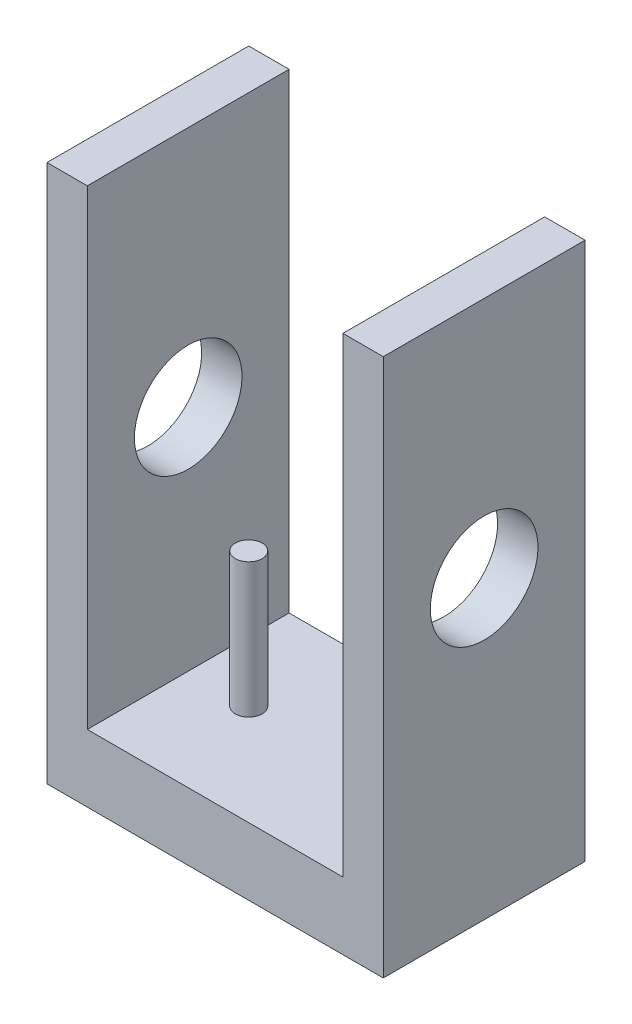
SolidWorks part; units mm, degrees
ref_plane "Plan de face" through (0, 0, 0) normal (0, 0, 1) x (1, 0, 0)
ref_plane "Plan de dessus" through (0, 0, 0) normal (0, 1, 0) x (1, 0, 0)
ref_plane "Plan de droite" through (0, 0, 0) normal (1, 0, 0) x (0, 0, -1)
sketch "Esquisse1" plane through (0, 0, 0) normal (0, 0, 1) x (1, 0, 0)
  line L1 (0, 0) -> (25, 0)
  line L2 (0, 0) -> (0, -40)
  line L3 (0, -40) -> (25, -40)
  line L4 (25, 0) -> (25, -40)
  dimension "D1" = 40
  dimension "D2" = 25
extrude "Boss.-Extru.2" add sketch "Esquisse1" along normal blind 15
sketch "Esquisse3" plane through (0, 0, 0) normal (0, 0, 1) x (1, 0, 0)
  line L0 (25, 0) -> (0, 0) construction
  line L1 (3, 0) -> (22, 0)
  line L2 (3, 0) -> (3, -35)
  line L3 (3, -35) -> (22, -35)
  line L4 (22, 0) -> (22, -35)
  line L5 (0, 0) -> (0, -40) construction
  line L6 (25, -40) -> (25, 0) construction
  line L7 (0, -40) -> (25, -40) construction
  dimension "D1" = 3
  dimension "D2" = 3
  dimension "D3" = 5
extrude "Enlèv. mat.-Extru.4" cut sketch "Esquisse3" along normal through all
sketch "Esquisse4" plane through (0, -35, 0) normal (0, 1, 0) x (1, 0, 0)
  line L0 (25, -15) -> (25, 0) construction
  line L2 (3, -15) -> (22, -15) construction
  circle A0 centre (7.5, -7.5) radius 1
  dimension "D1" = 2
  dimension "D2" = 17.5
  dimension "D3" = 7.5
extrude "Boss.-Extru.3" add sketch "Esquisse4" along normal blind 10
sketch "Esquisse5" plane through (0, 0, 0) normal (-1, 0, 0) x (0, 0, 1)
  line L0 (0, 0) -> (0, -40) construction
  circle A0 centre (7.5, -18) radius 4
  dimension "D1" = 22
  dimension "8" = 8
  dimension "D2" = 7.5
extrude "Enlèv. mat.-Extru.5" cut sketch "Esquisse5" against normal through all
